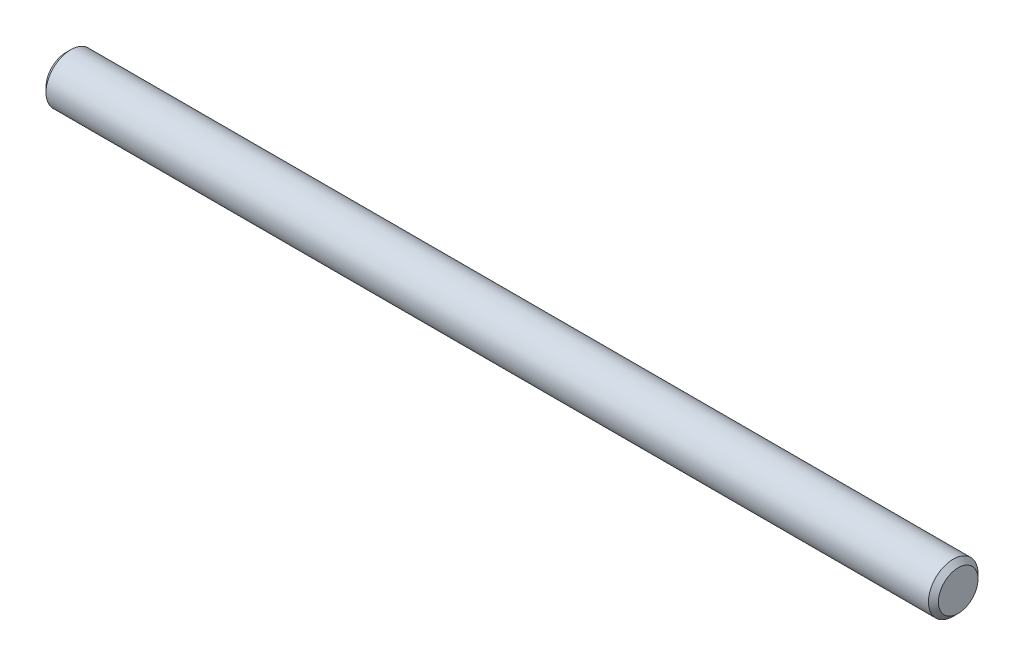
SolidWorks part; units mm, degrees
material "Stainless Steel (ferritic)"
ref_plane "Front Plane" through (0, 0, 0) normal (0, 0, 1) x (1, 0, 0)
ref_plane "Top Plane" through (0, 0, 0) normal (0, 1, 0) x (1, 0, 0)
ref_plane "Right Plane" through (0, 0, 0) normal (1, 0, 0) x (0, 0, -1)
sketch "Sketch1" plane through (0, 0, 0) normal (0, 0, 1) x (1, 0, 0)
  line L0 (-18, 0) -> (18, 0) construction
  line L2 (-18, 0) -> (18, 0)
  line L3 (-18, 0) -> (-18, 1)
  line L4 (-18, 1) -> (18, 1)
  line L5 (18, 0) -> (18, 1)
  point P3 (0, 0)
  dimension "D1" = 36
  dimension "D2" = 1
revolve "Revolve1" add sketch "Sketch1" angle 360 about L0
chamfer "Chamfer1" distance 0.2 angle 45 2 edges at (-18, -1, 0) (18, -1, 0)
